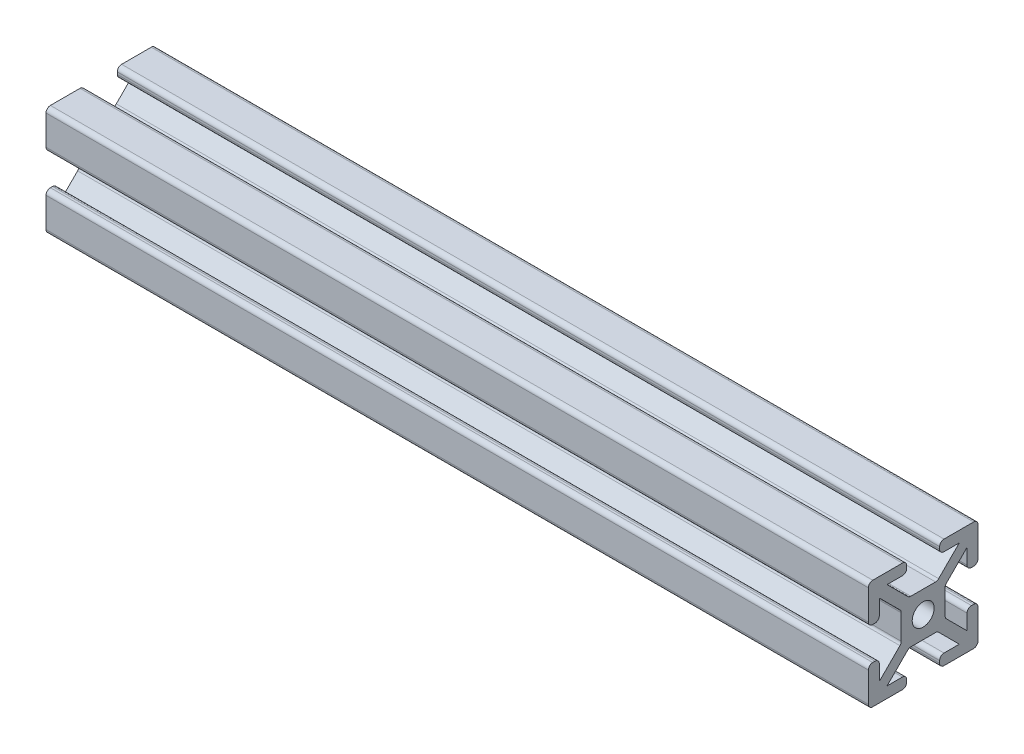
SolidWorks part; units mm, degrees
material "1060 Alloy"
ref_plane "Front Plane" through (0, 0, 0) normal (0, 0, 1) x (1, 0, 0)
ref_plane "Top Plane" through (0, 0, 0) normal (0, 1, 0) x (1, 0, 0)
ref_plane "Right Plane" through (0, 0, 0) normal (1, 0, 0) x (0, 0, -1)
sketch "Sketch1" plane through (0, 0, 0) normal (0, 1, 0) x (1, 0, 0)
  line L0 (0, 0) -> (150, 0)
other "Size 4X4 (1)"
ref_plane "Plane4" through (0, 0, 0) normal (1, 0, 0) x (0, 0, -1)
sketch "Sketch11" plane through (0, 0, 0) normal (1, 0, 0) x (0, 0, -1)
  line L0 (-3, 9.2) -> (-3, 8.8)
  line L1 (-2.2544, 4) -> (2.2544, 4)
  line L2 (-4, 2.2544) -> (-4, -2.2544)
  line L3 (-2.2544, -4) -> (2.2544, -4)
  line L4 (4, 2.2544) -> (4, -2.2544)
  line L7 (-6.5858, 8) -> (-3.8, 8)
  line L8 (-8, 6.5858) -> (-8, 3.8)
  line L9 (-6.5858, -8) -> (-3.8, -8)
  line L10 (8, 6.5858) -> (8, 3.8)
  line L12 (9.7657, -9.7657) -> (10, -10) construction
  line L13 (-9.2, 10) -> (-3.8, 10)
  line L14 (-10, 9.2) -> (-10, 3.8)
  line L15 (-9.2, -10) -> (-3.8, -10)
  line L16 (10, 9.2) -> (10, 3.8)
  line L17 (-10, 10) -> (-9.7657, 9.7657) construction
  line L18 (-10, -10) -> (-9.7657, -9.7657) construction
  line L21 (3, 9.2) -> (3, 8.8)
  line L22 (3, -9.2) -> (3, -8.8)
  line L23 (-3, -9.2) -> (-3, -8.8)
  line L24 (3.8, 10) -> (9.2, 10)
  line L25 (3.8, 8) -> (6.5858, 8)
  line L26 (-9.2, 3) -> (-8.8, 3)
  line L27 (9.2, 3) -> (8.8, 3)
  line L28 (9.2, -3) -> (8.8, -3)
  line L29 (-9.2, -3) -> (-8.8, -3)
  line L30 (-10, -3.8) -> (-10, -9.2)
  line L31 (-8, -3.8) -> (-8, -6.5858)
  line L32 (8, -3.8) -> (8, -6.5858)
  line L33 (10, -3.8) -> (10, -9.2)
  line L34 (3.8, -8) -> (6.5858, -8)
  line L35 (3.8, -10) -> (9.2, -10)
  line L36 (6.5858, 8) -> (2.8201, 4.2343)
  line L37 (8, 6.5858) -> (4.2343, 2.8201)
  line L38 (8, -6.5858) -> (4.2343, -2.8201)
  line L39 (6.5858, -8) -> (2.8201, -4.2343)
  line L40 (-6.5858, -8) -> (-2.8201, -4.2343)
  line L41 (-8, -6.5858) -> (-4.2343, -2.8201)
  line L42 (-8, 6.5858) -> (-4.2343, 2.8201)
  line L43 (-6.5858, 8) -> (-2.8201, 4.2343)
  line L47 (9.7657, 9.7657) -> (10, 10) construction
  circle A0 centre (0, 0) radius 2
  arc A1 (9.2, -3) -> (10, -3.8) centre (9.2, -3.8) cw
  arc A2 (8.8, -3) -> (8, -3.8) centre (8.8, -3.8) ccw
  arc A3 (3, -9.2) -> (3.8, -10) centre (3.8, -9.2) ccw
  arc A4 (3, -8.8) -> (3.8, -8) centre (3.8, -8.8) cw
  arc A5 (-3, -9.2) -> (-3.8, -10) centre (-3.8, -9.2) cw
  arc A6 (-3, -8.8) -> (-3.8, -8) centre (-3.8, -8.8) ccw
  arc A7 (-8.8, -3) -> (-8, -3.8) centre (-8.8, -3.8) cw
  arc A8 (-9.2, -3) -> (-10, -3.8) centre (-9.2, -3.8) ccw
  arc A9 (-10, -9.2) -> (-9.2, -10) centre (-9.2, -9.2) ccw
  arc A10 (9.2, -10) -> (10, -9.2) centre (9.2, -9.2) ccw
  arc A11 (9.2, 10) -> (10, 9.2) centre (9.2, 9.2) cw
  arc A12 (-9.2, 10) -> (-10, 9.2) centre (-9.2, 9.2) ccw
  arc A13 (9.2, 3) -> (10, 3.8) centre (9.2, 3.8) ccw
  arc A14 (8.8, 3) -> (8, 3.8) centre (8.8, 3.8) cw
  arc A15 (3, 9.2) -> (3.8, 10) centre (3.8, 9.2) cw
  arc A16 (3, 8.8) -> (3.8, 8) centre (3.8, 8.8) ccw
  arc A17 (-3, 9.2) -> (-3.8, 10) centre (-3.8, 9.2) ccw
  arc A18 (-3, 8.8) -> (-3.8, 8) centre (-3.8, 8.8) cw
  arc A19 (-8.8, 3) -> (-8, 3.8) centre (-8.8, 3.8) ccw
  arc A20 (-9.2, 3) -> (-10, 3.8) centre (-9.2, 3.8) cw
  arc A21 (-2.8201, 4.2343) -> (-2.2544, 4) centre (-2.2544, 4.8) ccw
  arc A22 (4.2343, 2.8201) -> (4, 2.2544) centre (4.8, 2.2544) ccw
  arc A23 (2.8201, 4.2343) -> (2.2544, 4) centre (2.2544, 4.8) cw
  arc A24 (4.2343, -2.8201) -> (4, -2.2544) centre (4.8, -2.2544) cw
  arc A25 (2.8201, -4.2343) -> (2.2544, -4) centre (2.2544, -4.8) ccw
  arc A26 (-2.8201, -4.2343) -> (-2.2544, -4) centre (-2.2544, -4.8) cw
  arc A27 (-4.2343, -2.8201) -> (-4, -2.2544) centre (-4.8, -2.2544) ccw
  arc A28 (-4.2343, 2.8201) -> (-4, 2.2544) centre (-4.8, 2.2544) cw
  point P7 (0, 0)
  point P10 (-2.5858, 4)
  point P53 (10, -3)
  point P56 (8, -3)
  point P59 (3, -10)
  point P62 (3, -8)
  point P65 (-3, -10)
  point P68 (-3, -8)
  point P71 (-8, -3)
  point P74 (-10, -3)
  point P89 (10, 3)
  point P92 (8, 3)
  point P95 (3, 10)
  point P98 (3, 8)
  point P101 (-3, 10)
  point P104 (-3, 8)
  point P107 (-8, 3)
  point P110 (-10, 3)
  point P116 (4, 2.5858)
  point P119 (2.5858, 4)
  point P122 (4, -2.5858)
  point P125 (2.5858, -4)
  point P128 (-2.5858, -4)
  point P131 (-4, -2.5858)
  point P134 (-4, 2.5858)
  dimension "D3" = 4
  dimension "D11" = 0.8
  dimension "D12" = 0.8
  dimension "D2" = 0.8
  dimension "D4" = 20
  dimension "D6" = 20
  dimension "D8" = 7
  dimension "D9" = 7
